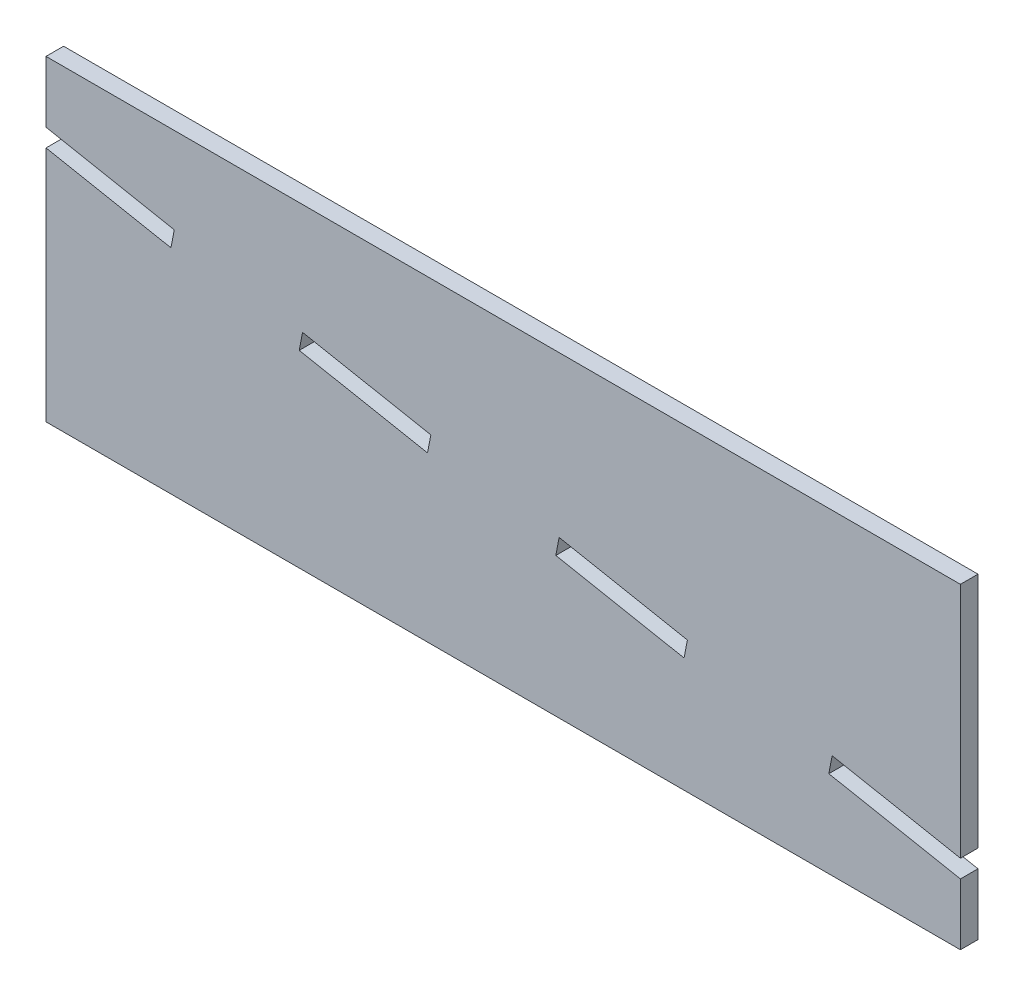
SolidWorks part; units mm, degrees
material "Contreplaqué pin"
ref_plane "Plan de face" through (0, 0, 0) normal (0, 0, 1) x (1, 0, 0)
ref_plane "Plan de dessus" through (0, 0, 0) normal (0, 1, 0) x (1, 0, 0)
ref_plane "Plan de droite" through (0, 0, 0) normal (1, 0, 0) x (0, 0, -1)
sketch "Esquisse1" plane through (0, 0, 0) normal (0, 0, 1) x (1, 0, 0)
  line L0 (0, 70) -> (260, 20) construction
  line L1 (0, 0) -> (260, 0)
  line L2 (0, 0) -> (0, 67.4542)
  line L3 (0, 90) -> (260, 90)
  line L4 (260, 0) -> (260, 17.4542)
  line L6 (0, 67.4542) -> (35.5303, 60.6214)
  line L7 (35.5303, 60.6214) -> (36.0024, 63.0765)
  line L8 (36.0024, 63.0765) -> (36.4745, 65.5315)
  line L9 (36.4745, 65.5315) -> (0, 72.5458)
  line L11 (72.4769, 56.0621) -> (72.9491, 58.5171)
  line L12 (72.9491, 58.5171) -> (109.4236, 51.5028)
  line L13 (109.4236, 51.5028) -> (108.9515, 49.0478)
  line L14 (108.9515, 49.0478) -> (108.4793, 46.5928)
  line L15 (108.4793, 46.5928) -> (72.0048, 53.6071)
  line L16 (72.0048, 53.6071) -> (72.4769, 56.0621)
  line L17 (145.426, 42.0335) -> (145.8981, 44.4885)
  line L18 (145.8981, 44.4885) -> (182.3726, 37.4741)
  line L19 (182.3726, 37.4741) -> (181.9005, 35.0191)
  line L20 (181.9005, 35.0191) -> (181.4284, 32.5641)
  line L21 (181.4284, 32.5641) -> (144.9539, 39.5784)
  line L22 (144.9539, 39.5784) -> (145.426, 42.0335)
  line L23 (223.0534, 27.1051) -> (223.5255, 29.5601)
  line L24 (223.5255, 29.5601) -> (260, 22.5458)
  line L27 (260, 17.4542) -> (222.5812, 24.6501)
  line L28 (222.5812, 24.6501) -> (223.0534, 27.1051)
  line L29 (0, 72.5458) -> (0, 90)
  line L30 (260, 22.5458) -> (260, 90)
  point P8 (0, 0)
  point P28 (0, 0)
  point P31 (0, 0)
  point P32 (0, 0)
  point P33 (0, 0)
  point P34 (225, 46.6506)
  point P35 (316.4079, 55.9914)
  point P36 (259.2849, 60.6715)
  point P37 (151.5621, 70.7142)
  dimension "D1" = 90
  dimension "30" = 20
  dimension "D3" = 20
  dimension "D4" = 260
  dimension "D5" = 5
  dimension "D6" = 37.1429
  dimension "D7" = 37.1429
  dimension "D8" = 37.1429
extrude "Boss.-Extru.1" add sketch "Esquisse1" along normal blind 5
equation "\"D6@Esquisse1\"=\"D4@Esquisse1\"/7"
equation "\"D7@Esquisse1\"=\"D4@Esquisse1\"/7"
equation "\"D8@Esquisse1\"=\"D7@Esquisse1\""
